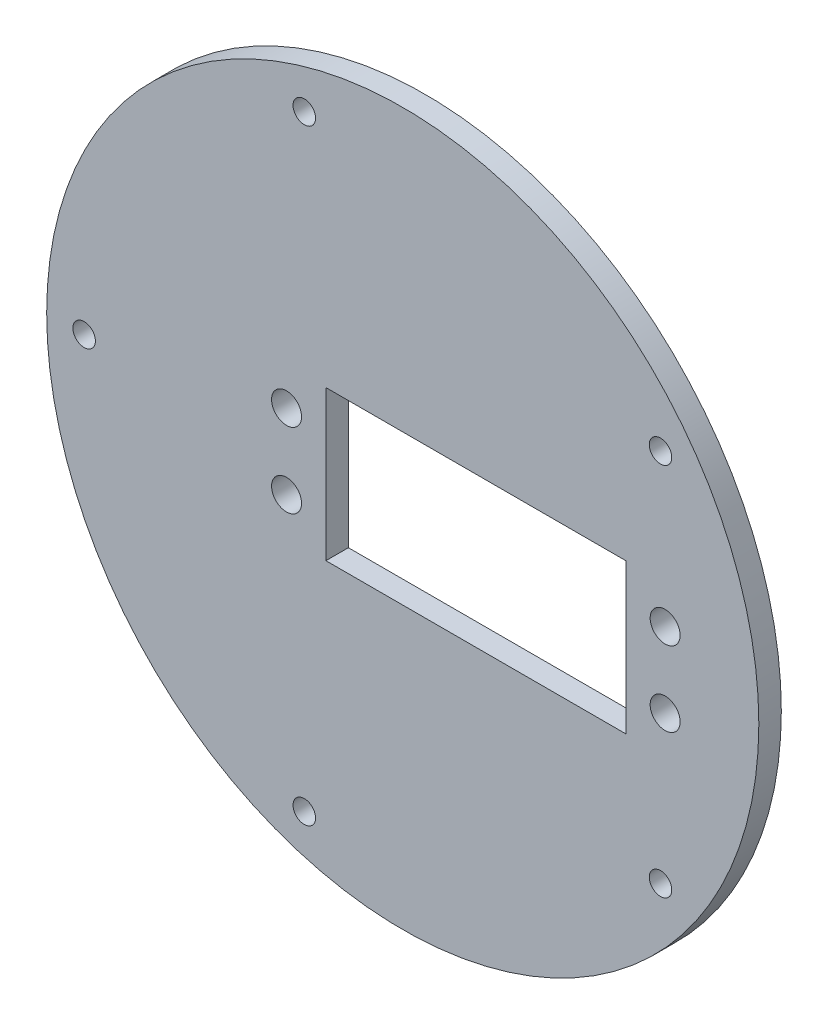
SolidWorks part; units mm, degrees
ref_plane "Alzado" through (0, 0, 0) normal (0, 0, 1) x (1, 0, 0)
ref_plane "Planta" through (0, 0, 0) normal (0, 1, 0) x (1, 0, 0)
ref_plane "Vista lateral" through (0, 0, 0) normal (1, 0, 0) x (0, 0, -1)
sketch "Croquis1" plane through (0, 0, 0) normal (0, 0, 1) x (1, 0, 0)
  circle A0 centre (0, 0) radius 47.5
  dimension "D1" = 95
extrude "Saliente-Extruir1" add sketch "Croquis1" along normal blind 3
sketch "Croquis2" plane through (0, 0, 3) normal (0, 0, 1) x (1, 0, 0)
  line L0 (37.5, 10) -> (-18, 10)
  line L1 (37.5, 10) -> (37.5, -10)
  line L2 (37.5, -10) -> (-18, -10)
  line L3 (-18, 10) -> (-18, -10)
  line L4 (37.5, 10) -> (-18, -10) construction
  line L5 (37.5, -10) -> (-18, 10) construction
  line L6 (-18, 0) -> (0, 0) construction
  circle A0 centre (-15.5, 5) radius 2
  circle A1 centre (-15.5, -5) radius 2
  circle A2 centre (35, 5) radius 2
  circle A3 centre (35, -5) radius 2
  point P0 (9.75, 0)
  dimension "D1" = 18
sketch "Croquis3" plane through (0, 0, 3) normal (0, 0, 1) x (1, 0, 0)
  line L0 (37.5, 10) -> (-18, 10) construction
  line L5 (29.75, -10) -> (-10.25, -10)
  line L6 (29.75, -10) -> (29.75, 10)
  line L7 (29.75, 10) -> (-10.25, 10)
  line L8 (-10.25, -10) -> (-10.25, 10)
  line L9 (29.75, -10) -> (-10.25, 10) construction
  line L10 (29.75, 10) -> (-10.25, -10) construction
  circle A0 centre (35, -5) radius 2 construction
  circle A1 centre (35, 5) radius 2 construction
  circle A4 centre (35, -5) radius 2
  circle A5 centre (35, 5) radius 2
  circle A8 centre (-15.5, -5) radius 2 construction
  circle A9 centre (-15.5, 5) radius 2 construction
  circle A10 centre (-15.5, -5) radius 2
  circle A11 centre (-15.5, 5) radius 2
  point P0 (9.75, 0)
  dimension "D1" = 40
extrude "Cortar-Extruir1" cut sketch "Croquis3" against normal through all
sketch "Croquis4" plane through (0, 0, 3) normal (0, 0, 1) x (1, 0, 0)
  circle A0 centre (0, 0) radius 42.5 construction
  circle A1 centre (-42.5, 0) radius 1.5
  circle A2 centre (-13.1332, 40.4199) radius 1.5
  circle A3 centre (0, 0) radius 42.5 construction
  circle A4 centre (34.3832, 24.9809) radius 1.5
  circle A5 centre (0, 0) radius 42.5 construction
  circle A6 centre (34.3832, -24.9809) radius 1.5
  circle A7 centre (0, 0) radius 42.5 construction
  circle A8 centre (-13.1332, -40.4199) radius 1.5
  circle A9 centre (0, 0) radius 42.5 construction
  point P20 (0, 0)
  dimension "D1" = 85
  dimension "D2" = 3
  dimension "D3" = 5
extrude "Cortar-Extruir2" cut sketch "Croquis4" against normal through all
